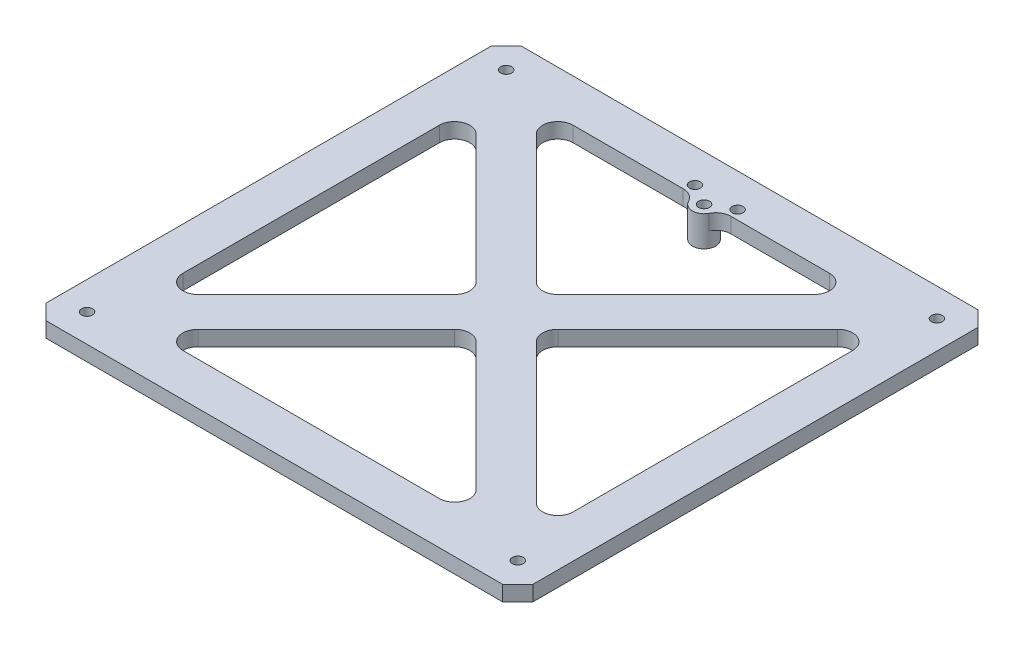
SolidWorks part; units mm, degrees
ref_plane "Front Plane" through (0, 0, 0) normal (0, 0, 1) x (1, 0, 0)
ref_plane "Top Plane" through (0, 0, 0) normal (0, 1, 0) x (1, 0, 0)
ref_plane "Right Plane" through (0, 0, 0) normal (1, 0, 0) x (0, 0, -1)
sketch "Sketch1" plane through (0, 0, 0) normal (0, 1, 0) x (1, 0, 0)
  line L0 (0, 192.024) -> (6.35, 198.374)
  line L1 (6.35, 0) -> (196.85, 0)
  line L2 (0, 6.35) -> (0, 192.024)
  line L3 (6.35, 198.374) -> (196.85, 198.374)
  line L4 (203.2, 6.35) -> (203.2, 192.024)
  line L5 (196.85, 198.374) -> (203.2, 192.024)
  line L6 (196.85, 0) -> (203.2, 6.35)
  line L7 (0, 6.35) -> (6.35, 0)
  point P0 (0, 0)
  point P1 (203.2, 198.374)
  point P2 (0, 198.374)
  point P3 (203.2, 0)
  dimension "D1" = 198.374
  dimension "D2" = 203.2
extrude "Boss-Extrude1" add sketch "Sketch1" along normal blind 6.35
sketch "Sketch2" plane through (0, 6.35, 0) normal (0, 1, 0) x (1, 0, 0)
  line L0 (203.2, 6.35) -> (203.2, 192.024) construction
  line L1 (45.6826, 180.594) -> (152.6914, 180.594)
  line L2 (17.78, 152.6914) -> (17.78, 45.6826)
  line L3 (45.6826, 17.78) -> (152.6914, 17.78)
  line L4 (185.42, 157.5174) -> (185.42, 40.8566)
  line L5 (196.85, 198.374) -> (6.35, 198.374) construction
  line L6 (0, 192.024) -> (0, 6.35) construction
  line L7 (0.762, 0.762) -> (197.612, 197.612) construction
  line L8 (3.175, 195.199) -> (99.187, 99.187) construction
  line L9 (28.6201, 157.1815) -> (82.1245, 103.6771)
  line L10 (41.1925, 28.6201) -> (94.6969, 82.1245)
  line L11 (41.1925, 169.7539) -> (94.6969, 116.2495)
  line L12 (28.6201, 41.1925) -> (82.1245, 94.6969)
  line L13 (7.0482, -5.5242) -> (203.8982, 191.3258) construction
  line L14 (-5.5242, 7.0482) -> (191.3258, 203.8982) construction
  line L15 (9.4612, 201.4852) -> (203.8982, 7.0482) construction
  line L16 (-3.1112, 188.9128) -> (191.3258, -5.5242) construction
  line L17 (116.2495, 103.6771) -> (174.5799, 162.0075)
  line L18 (99.187, 99.187) -> (197.612, 0.762) construction
  line L19 (3.175, 195.199) -> (197.612, 0.762) construction
  line L20 (116.2495, 94.6969) -> (174.5799, 36.3665)
  line L21 (103.6771, 116.2495) -> (157.1815, 169.7539)
  line L22 (103.6771, 82.1245) -> (157.1815, 28.6201)
  line L23 (6.35, 0) -> (196.85, 0) construction
  line L24 (6.35, 198.374) -> (0, 192.024) construction
  line L25 (203.2, 192.024) -> (196.85, 198.374) construction
  line L26 (196.85, 0) -> (203.2, 6.35) construction
  arc A0 (185.42, 40.8566) -> (174.5799, 36.3665) centre (179.07, 40.8566) cw
  arc A1 (185.42, 157.5174) -> (174.5799, 162.0075) centre (179.07, 157.5174) ccw
  arc A2 (152.6914, 180.594) -> (157.1815, 169.7539) centre (152.6914, 174.244) cw
  arc A3 (116.2495, 103.6771) -> (116.2495, 94.6969) centre (120.7396, 99.187) ccw
  arc A4 (41.1925, 28.6201) -> (45.6826, 17.78) centre (45.6826, 24.13) ccw
  arc A5 (152.6914, 17.78) -> (157.1815, 28.6201) centre (152.6914, 24.13) ccw
  arc A6 (28.6201, 41.1925) -> (17.78, 45.6826) centre (24.13, 45.6826) cw
  arc A7 (82.1245, 94.6969) -> (82.1245, 103.6771) centre (77.6344, 99.187) ccw
  arc A8 (28.6201, 157.1815) -> (17.78, 152.6914) centre (24.13, 152.6914) ccw
  arc A9 (41.1925, 169.7539) -> (45.6826, 180.594) centre (45.6826, 174.244) cw
  arc A10 (94.6969, 82.1245) -> (103.6771, 82.1245) centre (99.187, 77.6344) cw
  arc A11 (94.6969, 116.2495) -> (103.6771, 116.2495) centre (99.187, 120.7396) ccw
  point P10 (0, 99.187)
  point P11 (17.78, 99.187)
  point P37 (99.187, 17.78)
  point P40 (99.187, 99.187)
  point P50 (111.7594, 99.187)
  point P65 (99.187, 86.6146)
  point P68 (99.187, 111.7594)
  dimension "D7" = 6.35
  dimension "D8" = 6.35
  dimension "D9" = 6.35
  dimension "D1" = 17.78
  dimension "D2" = 17.78
  dimension "D3" = 8.89
  dimension "D5" = 17.78
  dimension "D6" = 17.78
  dimension "D4" = 8.89
extrude "Cut-Extrude1" cut sketch "Sketch2" against normal through all
sketch "Sketch3" plane through (0, 6.35, 0) normal (0, 1, 0) x (1, 0, 0)
  line L0 (6.35, 0) -> (196.85, 0) construction
  line L1 (0, 192.024) -> (0, 6.35) construction
  line L2 (203.2, 6.35) -> (203.2, 192.024) construction
  line L3 (196.85, 198.374) -> (6.35, 198.374) construction
  circle A0 centre (11.7373, 11.7373) radius 2.286
  circle A1 centre (191.4627, 11.7373) radius 2.286
  circle A2 centre (191.4627, 186.6367) radius 2.286
  circle A3 centre (11.7373, 186.6367) radius 2.286
  dimension "D1" = 2
  dimension "D3" = 4.572
  dimension "D4" = 11.7373
  dimension "D5" = 11.7373
  dimension "D6" = 11.7373
  dimension "D7" = 11.7373
  dimension "D8" = 11.7373
  dimension "D2" = 2
extrude "Cut-Extrude2" cut sketch "Sketch3" against normal through all
sketch "Sketch4" plane through (0, 6.35, 0) normal (0, 1, 0) x (1, 0, 0)
  line L0 (196.85, 198.374) -> (6.35, 198.374) construction
  line L1 (152.6914, 180.594) -> (45.6826, 180.594) construction
  line L3 (111.5547, 180.594) -> (91.6453, 180.594)
  circle A0 centre (101.6, 179.324) radius 2.286 construction
  arc A1 (97.3014, 177.1304) -> (105.8986, 177.1304) centre (101.6, 179.324) ccw
  arc A2 (97.3014, 177.1304) -> (91.6453, 180.594) centre (91.6453, 174.244) ccw
  arc A3 (111.5547, 180.594) -> (105.8986, 177.1304) centre (111.5547, 174.244) ccw
  point P5 (101.6, 198.374)
  dimension "D1" = 19.05
  dimension "D2" = 4.572
  dimension "D3" = 2.54
  dimension "D4" = 12.7
extrude "Boss-Extrude2" add sketch "Sketch4" against normal up to surface (6.35 mm away) up to face at (11.7373, 0, -184.3507)
sketch "Sketch5" plane through (0, 0, 0) normal (0, -1, 0) x (1, 0, 0)
  circle A0 centre (101.6, -179.324) radius 4.826
  arc A1 (105.8986, -177.1304) -> (97.3014, -177.1304) centre (101.6, -179.324) ccw construction
extrude "Boss-Extrude3" add sketch "Sketch5" along normal blind 6.35
sketch "Sketch6" plane through (0, -6.35, 0) normal (0, -1, 0) x (1, 0, 0)
  line L0 (92.71, -184.404) -> (110.49, -184.404) construction
  circle A0 centre (101.6, -179.324) radius 2.286
  circle A1 centre (92.71, -184.404) radius 2.286
  circle A2 centre (110.49, -184.404) radius 2.286
  point P7 (101.6, -184.404)
  dimension "D1" = 4.572
  dimension "D4" = 4.572
  dimension "D2" = 5.08
  dimension "D3" = 17.78
extrude "Cut-Extrude3" cut sketch "Sketch6" against normal through all contours A0 | A1 | A2
